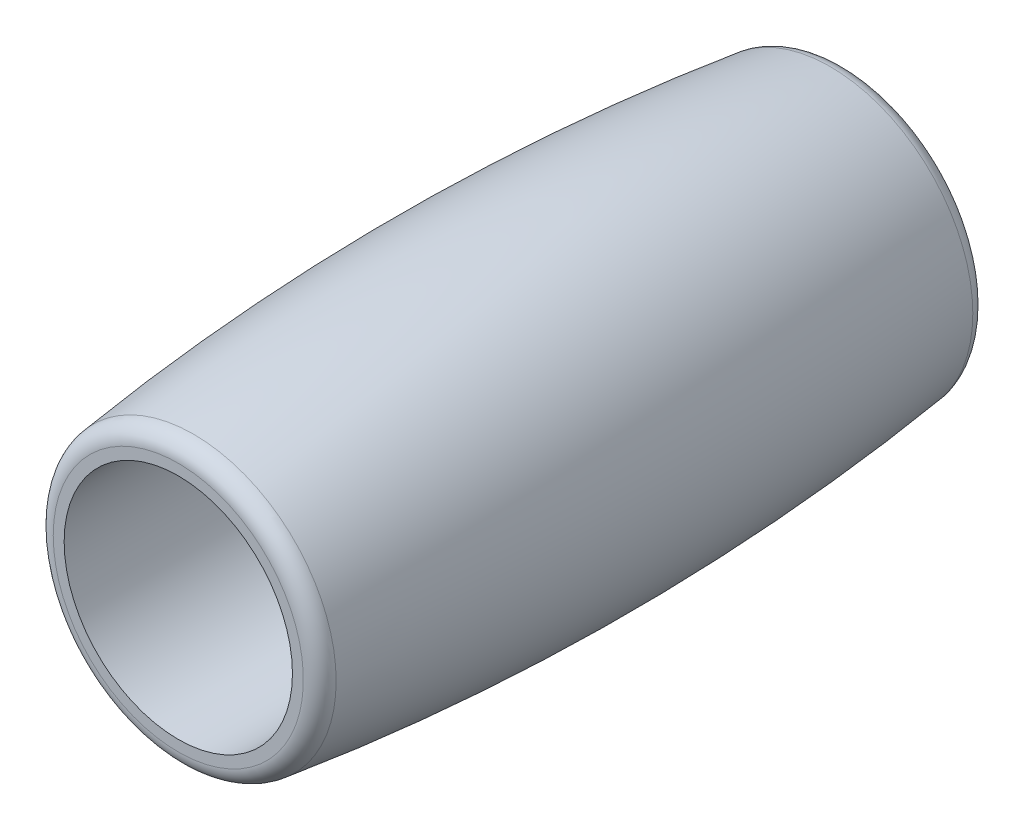
SolidWorks part; units mm, degrees
material "聚亚安酯(11671)"
ref_plane "前视基准面" through (0, 0, 0) normal (0, 0, 1) x (1, 0, 0)
ref_plane "上视基准面" through (0, 0, 0) normal (0, 1, 0) x (1, 0, 0)
ref_plane "右视基准面" through (0, 0, 0) normal (1, 0, 0) x (0, 0, -1)
sketch "草图1" plane through (0, 0, 0) normal (0, 1, 0) x (1, 0, 0)
  line L0 (8, 19.5971) -> (6.5, 19.5971)
  line L1 (6.5, -18.4029) -> (8, -18.4029)
  line L2 (0, 17.5604) -> (0, -20.5396) construction
  line L3 (-1.6667, 0) -> (9.929, 0) construction
  line L4 (-1.6667, 0) -> (-8.7509, 0) construction
  line L5 (6.5, 19.5971) -> (6.5, -18.4029)
  arc A0 (8, -18.4029) -> (8, 19.5971) centre (-135.775, 0.5971) ccw
  point P9 (9.25, 0.5971)
  point P12 (8, 0.5971)
  point P13 (0, 0)
  dimension "D1" = 38
  dimension "D2" = 9.25
  dimension "D4" = 6.5
  dimension "D5" = 8
  dimension "D6" = 6.5
  dimension "D7" = 8
revolve "旋转1" add sketch "草图1" angle 360 about L2
fillet "圆角1" radius 1 1 edges at (-8, 0, 18.4029)
fillet "圆角2" radius 1 1 edges at (-8, 0, -19.5971)
